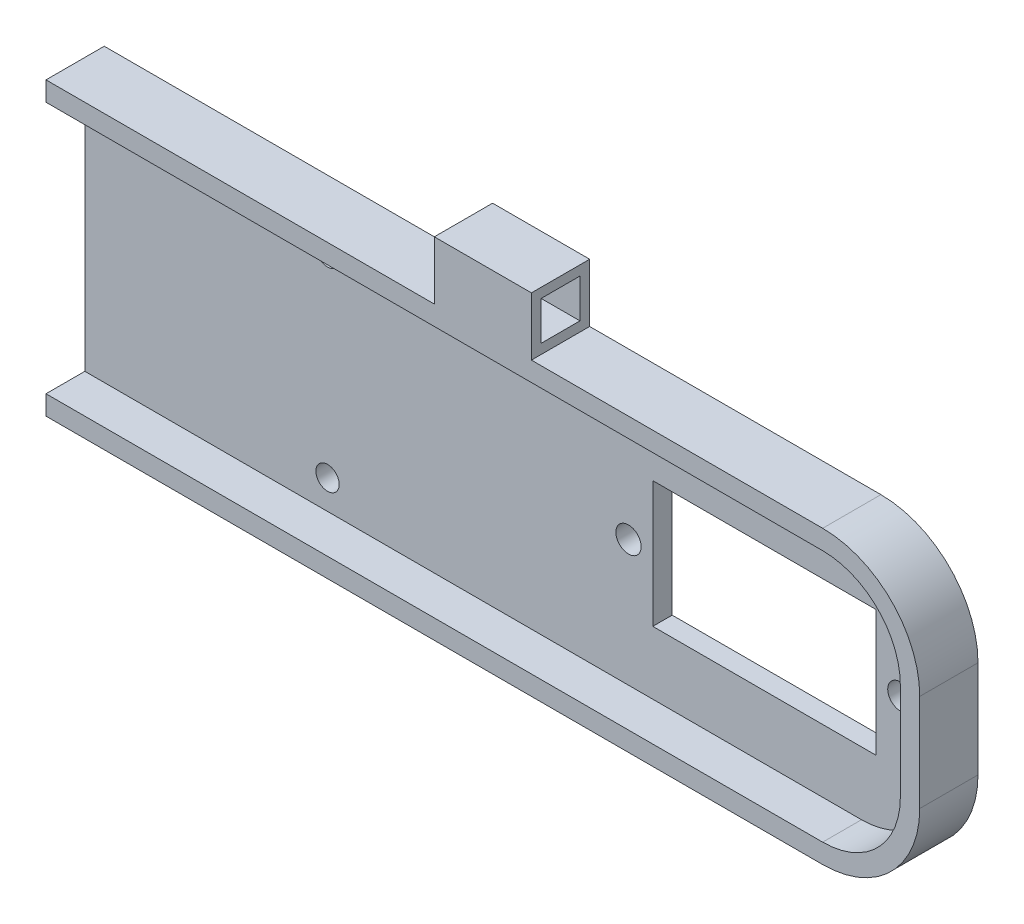
SolidWorks part; units mm, degrees
material "PLA"
ref_plane "Blat stołu" through (0, 0, 0) normal (0, 0, 1) x (1, 0, 0)
ref_plane "Płaszczyzna górna" through (0, 0, 0) normal (0, 1, 0) x (1, 0, 0)
ref_plane "Płaszczyzna prawa" through (0, 0, 0) normal (1, 0, 0) x (0, 0, -1)
sketch "Szkic1" plane through (0, 0, 0) normal (0, 0, 1) x (1, 0, 0)
  circle A3 centre (0, 0) radius 22.5
  dimension "D1" = 45
  dimension "D2" = 200
  dimension "D3" = 50
  dimension "D4" = 20
extrude "Dodanie-wyciągnięcie2" add sketch "Szkic1" along normal blind 13
sketch "Szkic2" plane through (0, 0, 0) normal (0, 0, 1) x (1, 0, 0)
  line L1 (-50, 15) -> (170, 15)
  line L2 (-50, 15) -> (-50, -15)
  line L3 (-50, -15) -> (170, -15)
  line L4 (170, 15) -> (170, -15)
  line L5 (-50, 15) -> (170, -15) construction
  line L6 (-50, -15) -> (170, 15) construction
  point P0 (60, 0)
  dimension "D1" = 30
  dimension "D2" = 50
  dimension "D3" = 220
extrude "Dodanie-wyciągnięcie3" add sketch "Szkic2" along normal blind 6
fillet "Zaokrąglenie1" radius 10 4 edges at (-50, -15, 3) (-50, 15, 3) (170, -15, 3) (170, 15, 3)
sketch "Szkic4" plane through (0, 0, 13) normal (0, 0, 1) x (1, 0, 0)
  circle A2 centre (0, 0) radius 20.5
  circle A3 centre (0, 0) radius 20.5
  dimension "D1" = 2
extrude "Wytnij-wyciągnięcie3" cut sketch "Szkic4" against normal blind 11
sketch "Szkic3" plane through (0, 0, 6) normal (0, 0, 1) x (1, 0, 0)
  line L3 (168, -5) -> (168, 5)
  line L4 (168, -5) -> (168, 5)
  line L5 (-48, 5) -> (-48, -5)
  line L6 (20.7666, -13) -> (160, -13)
  line L7 (-48, 5) -> (-48, -5)
  line L8 (160, 13) -> (20.7666, 13)
  line L9 (20.7666, -13) -> (160, -13)
  line L11 (160, 13) -> (20.7666, 13)
  line L14 (-20.7666, 13) -> (-40, 13)
  line L16 (-40, -13) -> (-20.7666, -13)
  line L17 (-20.7666, 13) -> (-40, 13)
  line L19 (-40, -13) -> (-20.7666, -13)
  arc A2 (20.7666, -13) -> (20.7666, 13) centre (0, 0) ccw
  arc A3 (20.7666, -13) -> (20.7666, 13) centre (0, 0) ccw
  arc A4 (-20.7666, 13) -> (-20.7666, -13) centre (0, 0) ccw
  arc A5 (-20.7666, 13) -> (-20.7666, -13) centre (0, 0) ccw
  arc A8 (160, -13) -> (168, -5) centre (160, -5) ccw
  arc A9 (160, -13) -> (168, -5) centre (160, -5) ccw
  arc A10 (168, 5) -> (160, 13) centre (160, 5) ccw
  arc A11 (168, 5) -> (160, 13) centre (160, 5) ccw
  arc A12 (-40, 13) -> (-48, 5) centre (-40, 5) ccw
  arc A13 (-40, 13) -> (-48, 5) centre (-40, 5) ccw
  arc A14 (-48, -5) -> (-40, -13) centre (-40, -5) ccw
  arc A15 (-48, -5) -> (-40, -13) centre (-40, -5) ccw
  dimension "D1" = 2
  dimension "D2" = 2
extrude "Wytnij-wyciągnięcie2" cut sketch "Szkic3" against normal blind 4
sketch "Szkic8" plane through (0, 0, 0) normal (0, 0, 1) x (1, 0, 0)
  line L1 (138.5, 6.5) -> (161.5, 6.5)
  line L2 (138.5, 6.5) -> (138.5, -6.5)
  line L3 (138.5, -6.5) -> (161.5, -6.5)
  line L4 (161.5, 6.5) -> (161.5, -6.5)
  line L5 (138.5, 6.5) -> (161.5, -6.5) construction
  line L6 (138.5, -6.5) -> (161.5, 6.5) construction
  point P0 (150, 0)
  dimension "D1" = 13
  dimension "D2" = 23
  dimension "D3" = 150
extrude "Wytnij-wyciągnięcie4" cut sketch "Szkic8" along normal up to next
sketch "Szkic12" plane through (0, 0, 2) normal (0, 0, 1) x (1, 0, 0)
  circle A0 centre (0, 0) radius 3.3
  dimension "D1" = 6.6
extrude "Dodanie-wyciągnięcie4" add sketch "Szkic12" along normal blind 3
hole_wizard "Otwór pod śrubę M21" positions "Szkic5" profile "Szkic6" hole size "M2" standard "ISO" end condition up to next
sketch "Szkic5" plane through (0, 0, 0) normal (0, 0, 1) x (1, 0, 0)
  point P0 (0, 0)
sketch "Szkic6" plane through (0, 0, 0) normal (1, 0, 0) x (0, 1, 0)
  line L0 (0, 0) -> (0, 5)
  line L1 (0, 5) -> (1.3, 5)
  line L2 (1.3, 5) -> (1.3, 0)
  line L5 (1.3, 0) -> (0, 0)
  line L11 (0, -6.35) -> (0, 107.95) construction
  dimension "Średnica otworu na wylot" = 2.6
  dimension "Głębokość otworu na wylot" = 5
hole_wizard "Otwór pod śrubę M23" positions "Szkic9" profile "Szkic10" hole size "M2" standard "ISO" end condition up to next
sketch "Szkic9" plane through (0, 0, 0) normal (0, 0, 1) x (1, 0, 0)
  line L0 (138.5, 6.5) -> (138.5, -6.5) construction
  point P0 (136, 0)
  point P2 (164, 0)
  dimension "D1" = 2.5
  dimension "D2" = 3
  dimension "D3" = 28
sketch "Szkic10" plane through (136, 0, 0) normal (1, 0, 0) x (0, 1, 0)
  line L0 (0, 0) -> (0, 2)
  line L1 (0, 2) -> (1.3, 2)
  line L2 (1.3, 2) -> (1.3, 0)
  line L5 (1.3, 0) -> (0, 0)
  line L11 (0, -6.35) -> (0, 107.95) construction
  dimension "Średnica otworu na wylot" = 2.6
  dimension "Głębokość otworu na wylot" = 2
sketch "Szkic14" plane through (0, 0, 2) normal (0, 0, 1) x (1, 0, 0)
  circle A0 centre (-40, 0) radius 3.3
  dimension "D1" = 40
  dimension "D2" = 40
extrude "Dodanie-wyciągnięcie5" add sketch "Szkic14" along normal blind 5
hole_wizard "Otwór pod śrubę M24" positions "Szkic 3D2" profile "Szkic11" hole size "M2" standard "ISO" end condition through all
sketch3d "Szkic 3D2"
  point P0 (-40, 0, 0)
  dimension "D1" = 40
sketch "Szkic11" plane through (-40, 0, 0) normal (1, 0, 0) x (0, 1, 0)
  line L0 (0, 0) -> (0, 13)
  line L1 (0, 13) -> (1.3, 13)
  line L2 (1.3, 13) -> (1.3, 0)
  line L5 (1.3, 0) -> (0, 0)
  line L11 (0, -6.35) -> (0, 107.95) construction
  dimension "Średnica otworu na wylot" = 2.6
  dimension "Głębokość otworu na wylot" = 13
ref_plane "Płaszczyzna1" through (130, 0, 0) normal (1, 0, 0) x (0, 0, -1)
sketch "Szkic15" plane through (130, 0, 0) normal (1, 0, 0) x (0, 0, -1)
  line L0 (-6, 15) -> (0, 15) construction
  line L1 (-6, 15) -> (0, 15)
  line L2 (-6, 15) -> (-6, 21)
  line L3 (-6, 21) -> (0, 21)
  line L4 (0, 15) -> (0, 21)
  line L5 (-6, 15) -> (0, 21) construction
  line L6 (-6, 21) -> (0, 15) construction
  line L7 (0, 5) -> (0, 15) construction
  line L8 (-6, 15) -> (-6, 5) construction
  line L9 (-5, 20) -> (-1, 20)
  line L10 (-1, 16) -> (-1, 20)
  line L11 (-5, 16) -> (-1, 16)
  line L12 (-5, 16) -> (-5, 20)
  point P0 (-3, 18)
  dimension "D1" = 6
  dimension "D2" = 1
extrude "Dodanie-wyciągnięcie6" add sketch "Szkic15" against normal blind 10
pattern_linear "Szyk liniowy1" count 2 spacing 70 along (-1, 0, 0) of "Dodanie-wyciągnięcie6"
sketch "Szkic17" plane through (0, 0, 2) normal (0, 0, 1) x (1, 0, 0)
  line L0 (50, 15) -> (16.7705, 15) construction
  line L1 (105, -10) -> (55, -10)
  line L2 (105, -10) -> (105, 10)
  line L3 (105, 10) -> (55, 10)
  line L4 (55, -10) -> (55, 10)
  line L5 (105, -10) -> (55, 10) construction
  line L6 (105, 10) -> (55, -10) construction
  point P0 (80, 0)
  dimension "D1" = 50
  dimension "D2" = 20
  dimension "D3" = 80
  dimension "D4" = 15
hole_wizard "Otwór pod śrubę M25" positions "Szkic18" profile "Szkic19" hole size "M2" standard "ISO" end condition through all
sketch "Szkic18" plane through (0, 0, 2) normal (0, 0, 1) x (1, 0, 0)
  point P0 (55, -10)
  point P3 (105, -10)
  point P6 (105, 10)
  point P9 (55, 10)
sketch "Szkic19" plane through (55, -10, 2) normal (1, 0, 0) x (0, -1, 0)
  line L0 (0, 0) -> (0, 2)
  line L1 (0, 2) -> (1.2, 2)
  line L2 (1.2, 2) -> (1.2, 0)
  line L5 (1.2, 0) -> (0, 0)
  line L11 (0, -6.35) -> (0, 107.95) construction
  dimension " rednica otworu na wylot" = 2.4
  dimension "G³êboko æ otworu na wylot" = 2
ref_plane "Płaszczyzna2" through (80, 0, 0) normal (1, 0, 0) x (0, 0, -1)
other "Cięcie powierzchnią1"
